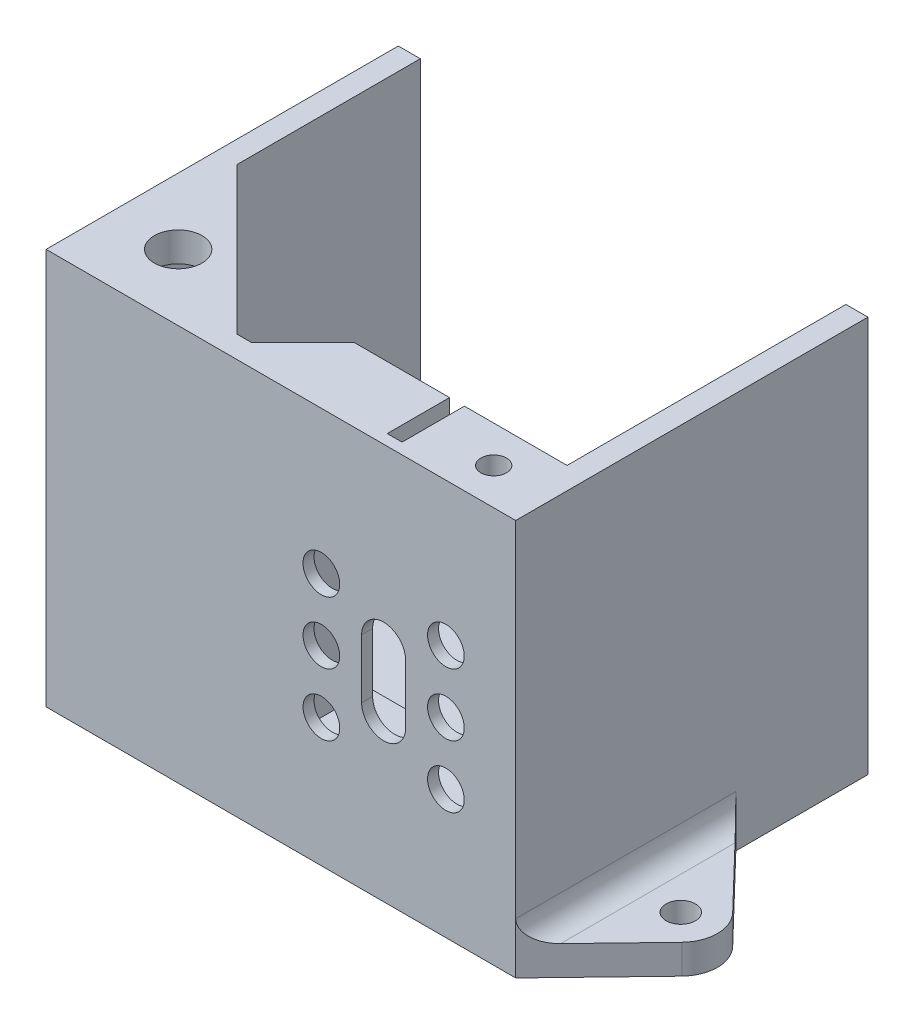
SolidWorks part; units mm, degrees
ref_plane "Płaszczyzna przednia" through (0, 0, 0) normal (0, 0, 1) x (1, 0, 0)
ref_plane "Płaszczyzna górna" through (0, 0, 0) normal (0, 1, 0) x (1, 0, 0)
ref_plane "Płaszczyzna prawa" through (0, 0, 0) normal (1, 0, 0) x (0, 0, -1)
sketch "Sketch1" plane through (0, 0, 0) normal (0, 1, 0) x (1, 0, 0)
  line L1 (-32, 24) -> (32, 24)
  line L2 (-32, 24) -> (-32, -24)
  line L3 (-32, -24) -> (32, -24)
  line L4 (32, 24) -> (32, -24)
  line L5 (-32, 24) -> (32, -24) construction
  line L6 (-32, -24) -> (32, 24) construction
  point P0 (0, 0)
  dimension "D1" = 64
  dimension "D2" = 48
extrude "Boss-Extrude1" add sketch "Sketch1" along normal blind 4
sketch "Sketch2" plane through (0, 0, 0) normal (0, -1, 0) x (1, 0, 0)
  line L9 (-20.6514, -16) -> (-22.3257, -13.1)
  line L10 (-22.3257, -13.1) -> (-25.6743, -13.1)
  line L11 (-25.6743, -13.1) -> (-27.3486, -16)
  line L12 (-27.3486, -16) -> (-25.6743, -18.9)
  line L13 (-25.6743, -18.9) -> (-22.3257, -18.9)
  line L14 (-22.3257, -18.9) -> (-20.6514, -16)
  line L15 (-32, -24) -> (-32, 24) construction
  line L16 (32, -24) -> (-32, -24) construction
  circle A0 centre (-24, -16) radius 2.9 construction
  dimension "D3" = 5.8
  dimension "D1" = 8
  dimension "D2" = 8
extrude "Cut-Extrude1" cut sketch "Sketch2" against normal blind 2.4
sketch "Sketch4" plane through (0, 0, 0) normal (0, -1, 0) x (1, 0, 0)
  line L0 (-32, -24) -> (-32, 24) construction
  line L1 (9.3486, 10) -> (7.6743, 12.9)
  line L2 (7.6743, 12.9) -> (4.3257, 12.9)
  line L3 (4.3257, 12.9) -> (2.6514, 10)
  line L4 (2.6514, 10) -> (4.3257, 7.1)
  line L5 (4.3257, 7.1) -> (7.6743, 7.1)
  line L6 (7.6743, 7.1) -> (9.3486, 10)
  line L8 (32, -24) -> (-32, -24) construction
  circle A0 centre (6, 10) radius 2.9 construction
  dimension "D3" = 5.8
  dimension "D1" = 38
  dimension "D2" = 34
extrude "Cut-Extrude2" cut sketch "Sketch4" against normal blind 2.4
sketch "Sketch6" plane through (0, 4, 0) normal (0, 1, 0) x (1, 0, 0)
  line L0 (-29, 21) -> (-29, 24)
  line L1 (-32, 24) -> (32, 24)
  line L2 (-32, 24) -> (-32, -24)
  line L3 (-32, -24) -> (32, -24)
  line L4 (32, 24) -> (32, -24)
  line L5 (-29, 21) -> (29, 21)
  line L6 (-29, 21) -> (-29, -21)
  line L7 (-29, -21) -> (29, -21)
  line L8 (29, 21) -> (29, -21)
  line L9 (-29, 21) -> (29, -21) construction
  line L10 (-29, -21) -> (29, 21) construction
  line L11 (29, 21) -> (29, 24)
  point P6 (0, 0)
  line M1 (32, -24) -> (32, 24)
  line M2 (32, 24) -> (-32, 24)
  line M3 (-32, 24) -> (-32, -24)
  line M4 (-32, -24) -> (32, -24)
  dimension "D1" = 58
  dimension "D2" = 42
extrude "Boss-Extrude3" add sketch "Sketch6" along normal blind 50 contours L11 L8 L7 L6 L0 M2 M3 M4 M1
sketch "Sketch9" plane through (0, 4, 0) normal (0, 1, 0) x (1, 0, 0)
  line L0 (1, -13) -> (-7, -21)
  line L3 (29, -13) -> (1, -13)
  line L5 (-29, -21) -> (29, -21) construction
  line L6 (-7, -21) -> (29, -21)
  line L7 (1, -13) -> (-7, -21)
  line L9 (29, -21) -> (29, -13)
  line M3 (29, -21) -> (29, 24)
  line M6 (-29, -21) -> (29, -21)
  dimension "D1" = 8
  dimension "D2" = 8
  dimension "D3" = 28
extrude "Boss-Extrude4" add sketch "Sketch9" along normal blind 50 contours L3 L0 M3 M6
sketch "Sketch10" plane through (0, 0, 13) normal (0, 0, -1) x (-1, 0, 0)
  line L0 (-29, 54) -> (-29, 4) construction
  line L1 (-26.75, 38.75) -> (-1.25, 38.75)
  line L2 (-26.75, 38.75) -> (-26.75, 13.25)
  line L3 (-26.75, 13.25) -> (-1.25, 13.25)
  line L4 (-1.25, 38.75) -> (-1.25, 13.25)
  line L5 (-26.75, 38.75) -> (-1.25, 13.25) construction
  line L6 (-26.75, 13.25) -> (-1.25, 38.75) construction
  line L7 (-14, 38.75) -> (-14, 54) construction
  line L9 (-29, 54) -> (-1, 54) construction
  line L15 (-15.0119, 38.75) -> (-12.9881, 38.75)
  line L16 (-15.0119, 38.75) -> (-15.0119, 54)
  line L17 (-15.0119, 54) -> (-12.9881, 54)
  line L18 (-12.9881, 38.75) -> (-12.9881, 54)
  line L19 (-15.0119, 38.75) -> (-12.9881, 54) construction
  line L20 (-15.0119, 54) -> (-12.9881, 38.75) construction
  point P0 (-14, 26)
  point P9 (-14, 46.375)
  line M5 (-1, 54) -> (-29, 54)
  dimension "D1" = 25.5
  dimension "D2" = 25.5
  dimension "D3" = 15
  dimension "D5" = 28
extrude "Cut-Extrude4" cut sketch "Sketch10" against normal blind 9.5 contours L1 L18 L16 M5 | L4 L1 L2 L3
sketch "Sketch13" plane through (0, 54, 0) normal (0, 1, 0) x (1, 0, 0)
  line L1 (29, -13) -> (-7.9463, -13)
  line L2 (29, -13) -> (29, -14)
  line L3 (29, -14) -> (-7.9463, -14)
  line L4 (-7.9463, -13) -> (-7.9463, -14)
  dimension "D1" = 1
extrude "Cut-Extrude6" cut sketch "Sketch13" against normal blind 32
sketch "Sketch15" plane through (0, 54, 0) normal (0, 1, 0) x (1, 0, 0)
  line L0 (-29, -1) -> (-9, -21)
  line L5 (-29, 24) -> (-29, -21) construction
  line L6 (-29, -21) -> (-7, -21) construction
  line L7 (-29, 24) -> (-29, -21) construction
  line L8 (-29, -1) -> (-29, -21)
  line L9 (-29, -21) -> (-9, -21)
  line L10 (-32, 24) -> (-32, -24) construction
  line L11 (-32, -24) -> (32, -24) construction
  circle A0 centre (-23, -15) radius 3.25
  dimension "D3" = 9
  dimension "D5" = 6.5
  dimension "D1" = 20
  dimension "D2" = 20
  dimension "D4" = 9
extrude "Boss-Extrude5" add sketch "Sketch15" against normal blind 4
sketch "Sketch17" plane through (0, 54, 0) normal (0, 1, 0) x (1, 0, 0)
  line L0 (32, -24) -> (32, 24) construction
  line L7 (-32, -24) -> (32, -24) construction
  line L8 (24, -19) -> (24, -24) construction
  line L9 (24, -19) -> (32, -19) construction
  line L11 (24, -15.6514) -> (21.1, -17.3257)
  line L12 (21.1, -17.3257) -> (21.1, -20.6743)
  line L13 (21.1, -20.6743) -> (24, -22.3486)
  line L14 (24, -22.3486) -> (26.9, -20.6743)
  line L15 (26.9, -20.6743) -> (26.9, -17.3257)
  line L16 (26.9, -17.3257) -> (24, -15.6514)
  circle A0 centre (24, -19) radius 2.9 construction
  dimension "D1" = 8
  dimension "D3" = 5.8
  dimension "D2" = 5
extrude "Cut-Extrude7" cut sketch "Sketch17" against normal blind 7
sketch "Sketch18" plane through (0, 0, 14) normal (0, 0, -1) x (-1, 0, 0)
  line L0 (-15.0119, 54) -> (-29, 54) construction
  line L1 (-26.9, 49.6) -> (-21.1, 49.6)
  line L2 (-26.9, 49.6) -> (-26.9, 47)
  line L3 (-26.9, 47) -> (-21.1, 47)
  line L4 (-21.1, 49.6) -> (-21.1, 47)
  line L5 (-32, 54) -> (-32, 0) construction
  point P6 (-24, 49.6)
  dimension "D1" = 7
  dimension "D2" = 2.6
  dimension "D3" = 5.8
  dimension "D4" = 8
extrude "Cut-Extrude8" cut sketch "Sketch18" against normal blind 5
sketch "Sketch19" plane through (0, 54, 0) normal (0, 1, 0) x (1, 0, 0)
  line L0 (25.75, -19) -> (22.25, -19) construction
  line L6 (22.25, -19) -> (24, -17.25) construction
  line L8 (24, -17.25) -> (24, -20.75) construction
  line L10 (20.7023, -15.4012) -> (27.2977, -15.4012)
  line L11 (20.7023, -15.4012) -> (20.7023, -22.5988)
  line L12 (20.7023, -22.5988) -> (27.2977, -22.5988)
  line L13 (27.2977, -15.4012) -> (27.2977, -22.5988)
  line L14 (20.7023, -22.5988) -> (27.2977, -22.5988)
  line L15 (20.7023, -22.5988) -> (20.7023, -15.4012)
  line L16 (20.7023, -15.4012) -> (27.2977, -15.4012)
  line L17 (27.2977, -22.5988) -> (27.2977, -15.4012)
  line L18 (20.7023, -22.5988) -> (27.2977, -15.4012) construction
  line L19 (20.7023, -15.4012) -> (27.2977, -22.5988) construction
  circle A0 centre (24, -19) radius 1.75
  line M1 (24, -15.6514) -> (26.9, -17.3257)
  line M2 (26.9, -17.3257) -> (26.9, -20.6743)
  line M3 (26.9, -20.6743) -> (24, -22.3486)
  line M4 (24, -22.3486) -> (21.1, -20.6743)
  line M5 (21.1, -20.6743) -> (21.1, -17.3257)
  line M6 (21.1, -17.3257) -> (24, -15.6514)
  dimension "D1" = 3.5
extrude "Boss-Extrude8" add sketch "Sketch19" against normal blind 4.4 contours A0 M1 M6 M5 M4 M3 M2
fillet "Fillet1" radius 1.5 2 edges at (-29, 50, 11) (-19, 50, 21)
sketch "Sketch20" plane through (0, 0, 0) normal (0, -1, 0) x (1, 0, 0)
  line L0 (32, 24) -> (43.1021, 12.4677)
  line L1 (39.5, 9) -> (32, 9) construction
  line L2 (32, -6) -> (43.1021, 5.5323)
  line L3 (-32, -24) -> (-42.9789, -14.5912)
  line L4 (32, -6) -> (32, 24)
  line L6 (-32, 2) -> (-32, -24)
  line L8 (-39.5, -11) -> (-32, -11) construction
  line L9 (-32, 2) -> (-42.9789, -7.4088)
  line L10 (-20.8246, -16) -> (-22.4123, -13.25) construction
  line L11 (-22.4123, -18.75) -> (-20.8246, -16) construction
  line L12 (-25.5877, -18.75) -> (-22.4123, -18.75) construction
  line L13 (-27.1754, -16) -> (-25.5877, -18.75) construction
  line L14 (-25.5877, -13.25) -> (-27.1754, -16) construction
  line L15 (-22.4123, -13.25) -> (-25.5877, -13.25) construction
  line L16 (9.1754, 10) -> (7.5877, 12.75) construction
  line L17 (7.5877, 7.25) -> (9.1754, 10) construction
  line L18 (4.4123, 7.25) -> (7.5877, 7.25) construction
  line L19 (2.8246, 10) -> (4.4123, 7.25) construction
  line L20 (4.4123, 12.75) -> (2.8246, 10) construction
  line L21 (7.5877, 12.75) -> (4.4123, 12.75) construction
  line L22 (-22.3257, -13.1) -> (-25.6743, -13.1) construction
  line L23 (-20.6514, -16) -> (-22.3257, -13.1) construction
  line L24 (-22.3257, -13.1) -> (-25.6743, -13.1) construction
  line L25 (-20.6514, -16) -> (-22.3257, -13.1) construction
  line L26 (32, -24) -> (32, 24)
  line L27 (32, 24) -> (-32, 24)
  line L28 (-32, 24) -> (-32, -24)
  line L29 (-32, -24) -> (32, -24)
  line L30 (32, -6) -> (32, 24)
  line L32 (-32, 2) -> (-32, -24)
  line L36 (9.3486, 10) -> (7.6743, 12.9)
  line L37 (7.6743, 7.1) -> (9.3486, 10)
  line L38 (4.3257, 7.1) -> (7.6743, 7.1)
  line L39 (2.6514, 10) -> (4.3257, 7.1)
  line L40 (4.3257, 12.9) -> (2.6514, 10)
  line L41 (7.6743, 12.9) -> (4.3257, 12.9)
  line L42 (9.3486, 10) -> (7.6743, 12.9) construction
  line L43 (7.6743, 7.1) -> (9.3486, 10) construction
  line L44 (4.3257, 7.1) -> (7.6743, 7.1) construction
  line L45 (2.6514, 10) -> (4.3257, 7.1) construction
  line L46 (4.3257, 12.9) -> (2.6514, 10) construction
  line L47 (7.6743, 12.9) -> (4.3257, 12.9) construction
  line L48 (-20.6514, -16) -> (-22.3257, -13.1)
  line L49 (-22.3257, -18.9) -> (-20.6514, -16)
  line L50 (-25.6743, -18.9) -> (-22.3257, -18.9)
  line L51 (-27.3486, -16) -> (-25.6743, -18.9)
  line L52 (-25.6743, -13.1) -> (-27.3486, -16)
  line L53 (-22.3257, -13.1) -> (-25.6743, -13.1)
  line L54 (-20.6514, -16) -> (-22.3257, -13.1) construction
  line L55 (-22.3257, -18.9) -> (-20.6514, -16) construction
  line L56 (-25.6743, -18.9) -> (-22.3257, -18.9) construction
  line L57 (-27.3486, -16) -> (-25.6743, -18.9) construction
  line L58 (-25.6743, -13.1) -> (-27.3486, -16) construction
  line L59 (-22.3257, -13.1) -> (-25.6743, -13.1) construction
  circle A0 centre (39.5, 9) radius 2
  circle A1 centre (-39.5, -11) radius 2
  arc A2 (43.1021, 5.5323) -> (43.1021, 12.4677) centre (39.5, 9) ccw
  arc A3 (-42.5162, -7.0122) -> (-42.5162, -14.9878) centre (-39.5, -11) ccw
  dimension "D1" = 0
  dimension "D2" = 0
  dimension "D3" = 0
extrude "Boss-Extrude9" add sketch "Sketch20" against normal blind 4 contours L9 A3 L3 L23 A1 | L2 A2 L0 L4 A0
fillet "Fillet2" radius 3 2 edges at (-32, 4, -11) (32, 4, 9)
sketch "Sketch22" plane through (0, 2.4, 0) normal (0, -1, 0) x (1, 0, 0)
  line L0 (4.3257, 12.9) -> (7.6743, 7.1) construction
  line L1 (7.6743, 7.1) -> (7.6743, 12.9) construction
  line L2 (7.6743, 12.9) -> (4.3257, 7.1) construction
  line L3 (-25.6743, -18.9) -> (-22.3257, -13.1) construction
  line L4 (-22.3257, -13.1) -> (-22.3257, -18.9) construction
  line L5 (-25.6743, -13.1) -> (-22.3257, -18.9) construction
  circle A0 centre (-24, -16) radius 1.75
  circle A1 centre (6, 10) radius 1.75
  dimension "D1" = 3.5
  dimension "D2" = 3.5
extrude "Cut-Extrude9" cut sketch "Sketch22" against normal blind 2
sketch "Sketch23" plane through (0, 0, 22.5) normal (0, 0, -1) x (-1, 0, 0)
  line L0 (-14, 13.25) -> (-14, 38.6846) construction
  line L1 (-26.75, 13.25) -> (-1.25, 13.25) construction
  line L2 (-14, 26) -> (-14, 22) construction
  line L3 (-14, 26) -> (-14, 30) construction
  line L4 (-14, 30) -> (-14, 22) construction
  line L5 (-11, 30) -> (-11, 22)
  line L6 (-17, 30) -> (-17, 22)
  line L7 (-14, 38.6846) -> (-14, 54) construction
  line L9 (-12.9881, 54) -> (-15.0119, 54) construction
  line L10 (-22.4853, 17.5147) -> (-5.5147, 17.5147) construction
  line L11 (-22.4853, 34.4853) -> (-22.4853, 17.5147) construction
  line L12 (-5.5147, 34.4853) -> (-5.5147, 17.5147) construction
  line L13 (-14, 26) -> (-1.25, 26) construction
  line L14 (-1.25, 38.75) -> (-1.25, 13.25) construction
  line L15 (-1.25, 26) -> (-26.75, 26) construction
  line L16 (-26.75, 38.75) -> (-26.75, 13.25) construction
  line L17 (-22.4853, 17.5147) -> (-22.4853, 34.4853) construction
  line L18 (-22.4853, 34.4853) -> (-5.5147, 34.4853) construction
  line L19 (-5.5147, 17.5147) -> (-5.5147, 34.4853) construction
  line L20 (-22.4853, 17.5147) -> (-5.5147, 34.4853) construction
  line L21 (-22.4853, 34.4853) -> (-5.5147, 17.5147) construction
  circle A1 centre (-22.4853, 34.4853) radius 2.5
  circle A2 centre (-5.5147, 34.4853) radius 2.5
  circle A3 centre (-5.5147, 17.5147) radius 2.5
  circle A4 centre (-22.4853, 17.5147) radius 2.5
  arc A6 (-11, 30) -> (-17, 30) centre (-14, 30) ccw
  arc A7 (-17, 22) -> (-11, 22) centre (-14, 22) ccw
  circle A8 centre (-22.4853, 26) radius 2.5
  circle A9 centre (-5.5147, 26) radius 2.5
  point P19 (-14, 26)
  point P37 (-14, 26)
  dimension "D5" = 5
  dimension "D6" = 5
  dimension "D7" = 12
  dimension "D8" = 12
  dimension "D2" = 5
  dimension "D3" = 5
  dimension "D1" = 5
  dimension "D4" = 5
extrude "Cut-Extrude10" cut sketch "Sketch23" against normal blind 3
sketch "Sketch24" plane through (29, 0, 0) normal (-1, 0, 0) x (0, 0, 1)
  line L0 (10, 54) -> (10, 8.8247) construction
  line L1 (-24, 54) -> (24, 54) construction
  line L2 (14, 54) -> (14, 22) construction
  line L3 (14, 22) -> (13, 22) construction
  line L4 (10, 22) -> (8, 22)
  line L5 (10, 22) -> (10, 32)
  line L6 (10, 32) -> (8, 32)
  line L7 (8, 22) -> (8, 32)
  line L8 (10, 22) -> (8, 32) construction
  line L9 (10, 32) -> (8, 22) construction
  point P10 (9, 27)
  dimension "D1" = 4
  dimension "D2" = 10
  dimension "D3" = 2
  dimension "D4" = 0
extrude "Boss-Extrude10" add sketch "Sketch24" along normal blind 4
sketch "Sketch25" plane through (0, 0, 21) normal (0, 0, -1) x (-1, 0, 0)
  line L0 (1, 48.5) -> (1, 10.3183) construction
  line L1 (29, 48.5) -> (9, 48.5) construction
  line L2 (-29, 32) -> (9.043, 32) construction
  line L3 (-29, 22) -> (-29, 4) construction
  line L4 (-29, 22) -> (-29, 54) construction
  line L5 (-25, 32) -> (-29, 32) construction
  line L6 (-29, 22) -> (9.043, 22) construction
  line L8 (3, 32) -> (1, 32)
  line L9 (3, 32) -> (3, 22)
  line L10 (3, 22) -> (1, 22)
  line L11 (1, 32) -> (1, 22)
  line L12 (3, 32) -> (1, 22) construction
  line L13 (3, 22) -> (1, 32) construction
  point P19 (2, 27)
  dimension "D1" = 30
  dimension "D2" = 2
  dimension "D3" = 10
extrude "Boss-Extrude11" add sketch "Sketch25" along normal blind 13
sketch "Sketch26" plane through (-1, 0, 0) normal (1, 0, 0) x (0, 0, -1)
  line L5 (-8, 22) -> (-15, 22) construction
  line L6 (-8, 32) -> (-10, 32)
  line L7 (-8, 32) -> (-8, 22)
  line L8 (-8, 22) -> (-10, 22)
  line L9 (-10, 32) -> (-10, 22)
  line L10 (-8, 32) -> (-10, 22) construction
  line L11 (-8, 22) -> (-10, 32) construction
  point P4 (-9, 27)
  dimension "D1" = 2
extrude "Boss-Extrude12" add sketch "Sketch26" along normal blind 4
fillet "Fillet4" radius 1 13 edges at (3, 32, 9) (-3, 32, 12.5) (-3, 22, 12.5) (0, 22, 8) (0, 32, 8) (-3, 27, 8) (25, 22, 9) (25, 32, 9) (25, 27, 8) (3, 22, 9) (3, 27, 8) (27, 22, 8) (27, 32, 8)
